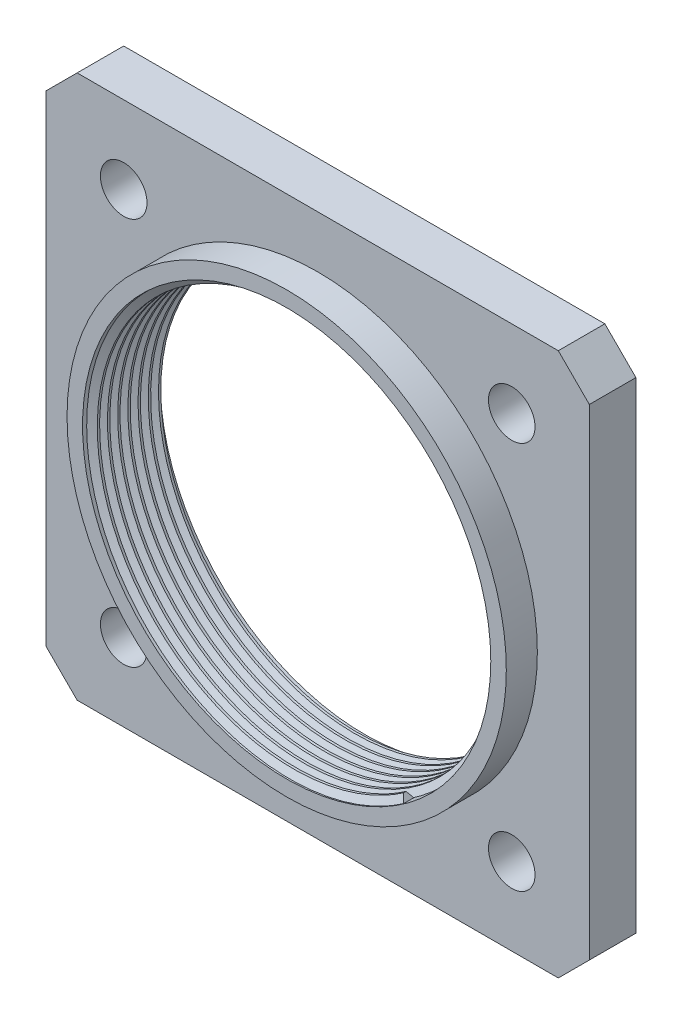
SolidWorks part; units mm, degrees
ref_plane "Front Plane" through (0, 0, 0) normal (0, 0, 1) x (1, 0, 0)
ref_plane "Top Plane" through (0, 0, 0) normal (0, 1, 0) x (1, 0, 0)
ref_plane "Right Plane" through (0, 0, 0) normal (1, 0, 0) x (0, 0, -1)
sketch "Sketch1" plane through (0, 0, 0) normal (0, 0, 1) x (1, 0, 0)
  line L1 (-17.5, 17.5) -> (17.5, 17.5)
  line L2 (-17.5, 17.5) -> (-17.5, -17.5)
  line L3 (-17.5, -17.5) -> (17.5, -17.5)
  line L4 (17.5, 17.5) -> (17.5, -17.5)
  line L5 (-17.5, 17.5) -> (17.5, -17.5) construction
  line L6 (-17.5, -17.5) -> (17.5, 17.5) construction
  line L7 (-12.5, 12.5) -> (12.5, 12.5) construction
  line L8 (-12.5, 12.5) -> (-12.5, -12.5) construction
  line L9 (-12.5, -12.5) -> (12.5, -12.5) construction
  line L10 (12.5, 12.5) -> (12.5, -12.5) construction
  line L11 (-12.5, 12.5) -> (12.5, -12.5) construction
  line L12 (-12.5, -12.5) -> (12.5, 12.5) construction
  circle A0 centre (-12.5, 12.5) radius 1.5
  circle A1 centre (12.5, 12.5) radius 1.5
  circle A2 centre (-12.5, -12.5) radius 1.5
  circle A3 centre (12.5, -12.5) radius 1.5
  circle A4 centre (0, 0) radius 13.15
  point P0 (0, 0)
  point P6 (0, 0)
  dimension "D3" = 3
  dimension "D4" = 26.3
  dimension "D1" = 35
  dimension "D2" = 25
extrude "Boss-Extrude1" add sketch "Sketch1" along normal blind 3
sketch "Sketch3" plane through (0, 0, 3) normal (0, 0, 1) x (1, 0, 0)
  circle A0 centre (0, 0) radius 13.15
  circle A1 centre (0, 0) radius 14.15
  circle A2 centre (0, 0) radius 13.15 construction
  dimension "D1" = 1
extrude "Boss-Extrude2" add sketch "Sketch3" along normal blind 2
chamfer "Chamfer1" distance 2 angle 45 4 edges at (17.5, 17.5, 1.5) (17.5, -17.5, 1.5) (-17.5, -17.5, 1.5) (-17.5, 17.5, 1.5)
sketch "Sketch4" plane through (0, 0, 0) normal (0, 0, -1) x (-1, 0, 0)
  circle A0 centre (0, 0) radius 13.145
  dimension "D1" = 26.29
curve "Helix/Spiral1" pitch 0.6572 height 4.5 turns 6.847
ref_plane "Plane1" through (7.5226, -10.7797, 4.5) normal (0.82, 0.5723, 0.008) x (0.0065, 0.0046, -1)
sketch "Sketch5" plane through (7.5226, -10.7797, 4.5) normal (0.82, 0.5723, 0.008) x (0.0065, 0.0046, -1)
  line L0 (-0.2277, 0.4434) -> (-0.0777, 0.4434)
  line L1 (-0.0777, 0.4434) -> (0.1723, 0.0104)
  line L2 (0.1723, 0.0104) -> (-0.4777, 0.0104)
  line L3 (-0.4777, 0.0104) -> (-0.2277, 0.4434)
  line L4 (-0.2277, 0.4434) -> (-0.1527, 0.0104) construction
  line L5 (-0.1527, 0.0104) -> (-0.0777, 0.4434) construction
  point P4 (0, 0)
  point P6 (-0.1527, 0.0104)
  point P7 (0, 0)
  point P8 (0.1723, 0.0104)
  point P9 (0, 0)
  dimension "D1" = 0.65
  dimension "D2" = 60
  dimension "D3" = 0.15
sweep "Sweep1" add profiles "Sketch5" path "Helix/Spiral1"
sketch "Sketch6" plane through (0, 0, 0) normal (0, 0, -1) x (-1, 0, 0)
  circle A0 centre (0, 0) radius 26.6171
extrude "Cut-Extrude1" cut sketch "Sketch6" along normal through all
